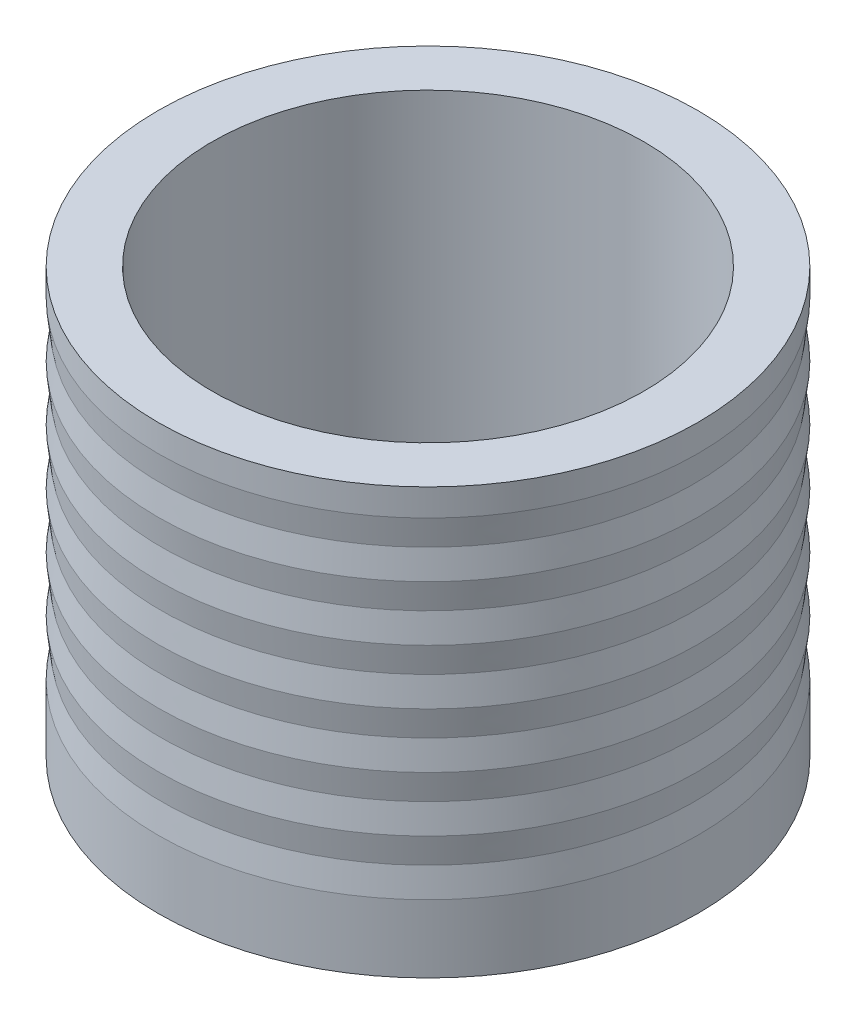
SolidWorks part; units mm, degrees
ref_plane "Front Plane" through (0, 0, 0) normal (0, 0, 1) x (1, 0, 0)
ref_plane "Top Plane" through (0, 0, 0) normal (0, 1, 0) x (1, 0, 0)
ref_plane "Right Plane" through (0, 0, 0) normal (1, 0, 0) x (0, 0, -1)
sketch "Sketch2" plane through (0, 0, 0) normal (0, 0, 1) x (1, 0, 0)
  line L0 (25.4, 0) -> (25.4, 50.0062)
  line L1 (25.4, 50.0062) -> (31.75, 50.0062)
  line L2 (31.75, 50.0062) -> (31.75, 0)
  line L3 (31.75, 0) -> (25.4, 0)
  line L4 (0, -40.6566) -> (0, 40.6566)
  point P8 (0, 0)
  dimension "D1" = 25.4
  dimension "D2" = 31.75
  dimension "D3" = 50.0062
revolve "Revolve1" add sketch "Sketch2" angle 360 about L4
sketch "Sketch3" plane through (0, 0, 0) normal (0, 0, 1) x (1, 0, 0)
  line L0 (31.75, 46.8312) -> (31.369, 43.5928)
  line L1 (31.75, 0) -> (31.75, 50.0062) construction
  line L2 (31.369, 43.5928) -> (31.75, 40.3542)
  line L3 (31.75, 46.8312) -> (31.75, 40.3542)
  line L4 (31.75, 50.0062) -> (-31.75, 50.0062) construction
  dimension "D1" = 0.381
  dimension "D2" = 6.477
  dimension "D3" = 3.175
revolve "Cut-Revolve1" cut sketch "Sketch3" angle 360 about L4
pattern_linear "LPattern1" count 6 spacing 6.477 along (0, -1, 0) of "Cut-Revolve1"
